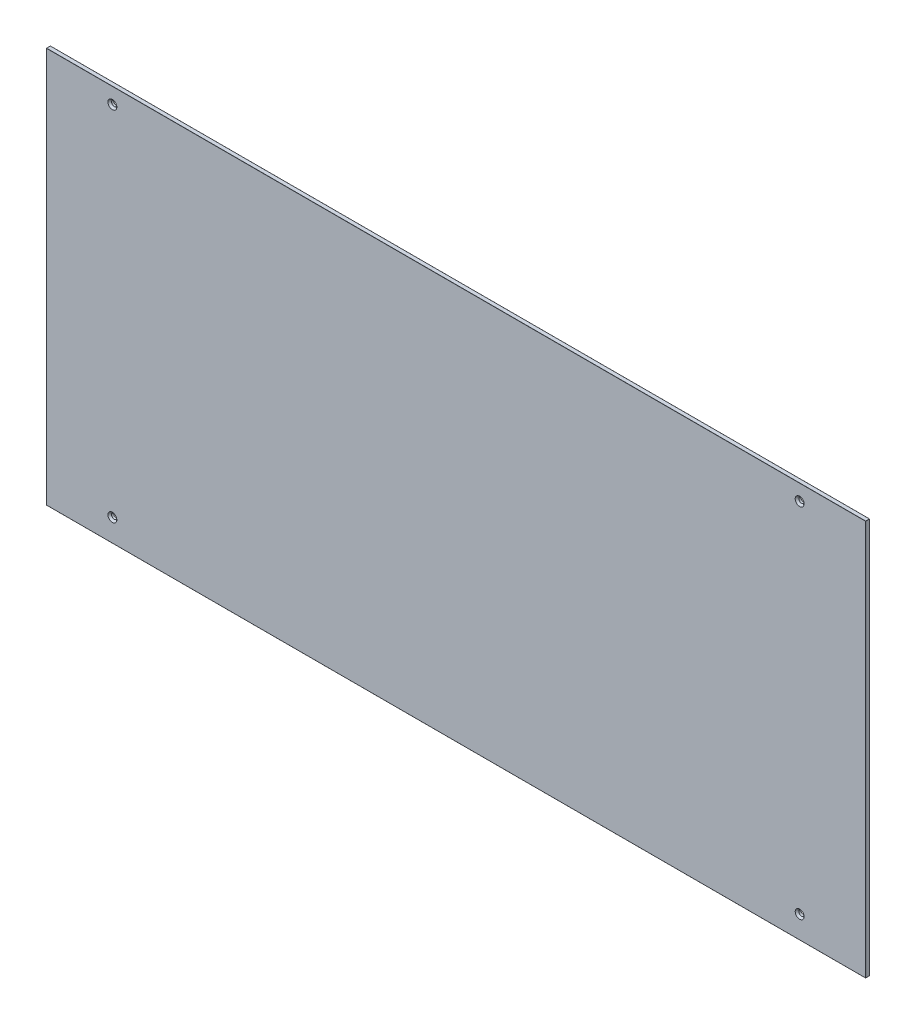
SolidWorks part; units mm, degrees
material "Glass"
ref_plane "Front Plane" through (0, 0, 0) normal (0, 0, 1) x (1, 0, 0)
ref_plane "Top Plane" through (0, 0, 0) normal (0, 1, 0) x (1, 0, 0)
ref_plane "Right Plane" through (0, 0, 0) normal (1, 0, 0) x (0, 0, -1)
sketch "Sketch1" plane through (0, 0, 0) normal (0, 0, 1) x (1, 0, 0)
  line L1 (-621, -300) -> (621, -300)
  line L2 (-621, -300) -> (-621, 300)
  line L3 (-621, 300) -> (621, 300)
  line L4 (621, -300) -> (621, 300)
  line L5 (-621, -300) -> (621, 300) construction
  line L6 (-621, 300) -> (621, -300) construction
  point P0 (0, 0)
  dimension "Largura" = 1242
  dimension "Altura" = 600
extrude "Boss-Extrude1" add sketch "Sketch1" along normal blind 6
sketch "Sketch2" plane through (0, 0, 6) normal (0, 0, 1) x (1, 0, 0)
  line L0 (-621, 300) -> (-621, -300) construction
  line L1 (621, -300) -> (621, 300) construction
  line L2 (621, 300) -> (-621, 300) construction
  line L3 (-621, -300) -> (621, -300) construction
  circle A0 centre (-521, 276) radius 4
  circle A1 centre (521, 276) radius 4
  circle A2 centre (521, -266) radius 4
  circle A3 centre (-521, -266) radius 4
  dimension "D1" = 8
  dimension "D2" = 100
  dimension "D3" = 100
  dimension "D4" = 24
  dimension "D5" = 34
extrude "Cut-Extrude1" cut sketch "Sketch2" against normal through all
chamfer "Chamfer1" distance 2.75 angle 45 4 edges at (-517, -266, 6) (525, -266, 6) (525, 276, 6) (-517, 276, 6)
fillet "Fillet1" radius 0.2 12 edges at (0, -300, 0) (621, 0, 0) (621, -300, 3) (0, -300, 6) (621, 0, 6) (621, 300, 3) (-621, -300, 3) (0, 300, 0) (-621, 0, 0) (0, 300, 6) (-621, 300, 3) (-621, 0, 6)
